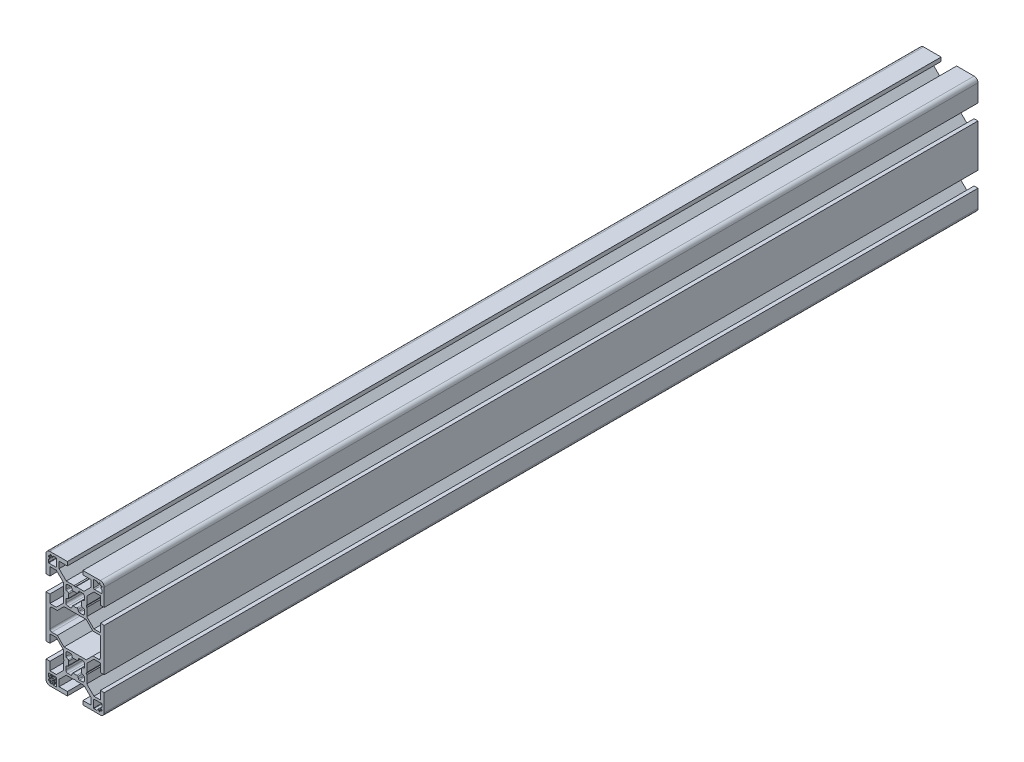
SolidWorks part; units mm, degrees
material "6063-T5"
ref_plane "Piano frontale" through (0, 0, 0) normal (0, 0, 1) x (1, 0, 0)
ref_plane "Piano superiore" through (0, 0, 0) normal (0, 1, 0) x (1, 0, 0)
ref_plane "Piano destro" through (0, 0, 0) normal (1, 0, 0) x (0, 0, -1)
ref_plane "Plane1" through (0, 0, -450) normal (0, 0, -1) x (-1, 0, 0)
sketch "Sketch1" plane through (0, 0, -450) normal (0, 0, -1) x (-1, 0, 0)
  line L0 (12.9, 28.5) -> (12.9, 28.2)
  line L1 (13.2, 27.9) -> (13.5, 27.9)
  line L2 (13.8, 27.6) -> (13.8, 27.4)
  line L3 (13.6, 27.2) -> (13.43, 27.2)
  line L4 (13.23, 27) -> (13.23, 26.6)
  line L5 (13.43, 26.4) -> (13.6, 26.4)
  line L6 (13.8, 26.2) -> (13.8, 24.7)
  line L7 (13.6, 24.5) -> (10, 24.5)
  line L8 (9.5, 25) -> (9.5, 28.6)
  line L9 (9.7, 28.8) -> (11.2, 28.8)
  line L10 (11.4, 28.6) -> (11.4, 28.43)
  line L11 (11.6, 28.23) -> (12, 28.23)
  line L12 (12.2, 28.43) -> (12.2, 28.6)
  line L13 (12.4, 28.8) -> (12.6, 28.8)
  line L14 (9.5, -28.6) -> (9.5, -25)
  line L15 (10, -24.5) -> (13.6, -24.5)
  line L16 (13.8, -24.7) -> (13.8, -26.2)
  line L17 (13.6, -26.4) -> (13.43, -26.4)
  line L18 (13.23, -26.6) -> (13.23, -27)
  line L19 (13.43, -27.2) -> (13.6, -27.2)
  line L20 (13.8, -27.4) -> (13.8, -27.6)
  line L21 (13.5, -27.9) -> (13.2, -27.9)
  line L22 (12.9, -28.2) -> (12.9, -28.5)
  line L23 (12.6, -28.8) -> (12.4, -28.8)
  line L24 (12.2, -28.6) -> (12.2, -28.43)
  line L25 (12, -28.23) -> (11.6, -28.23)
  line L26 (11.4, -28.43) -> (11.4, -28.6)
  line L27 (11.2, -28.8) -> (9.7, -28.8)
  line L28 (-5.7172, 9) -> (5.7172, 9)
  line L29 (9.1672, 5.55) -> (12, 5.55)
  line L30 (13, 4.55) -> (13, -4.55)
  line L31 (12, -5.55) -> (9.1672, -5.55)
  line L32 (5.7172, -9) -> (-5.7172, -9)
  line L33 (-9.1672, -5.55) -> (-12, -5.55)
  line L34 (-13, -4.55) -> (-13, 5.55)
  line L35 (-13, 5.55) -> (-9.1672, 5.55)
  line L36 (-11.2, 28.8) -> (-9.7, 28.8)
  line L37 (-9.5, 28.6) -> (-9.5, 25)
  line L38 (-10, 24.5) -> (-13.6, 24.5)
  line L39 (-13.8, 24.7) -> (-13.8, 26.2)
  line L40 (-13.6, 26.4) -> (-13.43, 26.4)
  line L41 (-13.23, 26.6) -> (-13.23, 27)
  line L42 (-13.43, 27.2) -> (-13.6, 27.2)
  line L43 (-13.8, 27.4) -> (-13.8, 27.6)
  line L44 (-13.5, 27.9) -> (-13.2, 27.9)
  line L45 (-12.9, 28.2) -> (-12.9, 28.5)
  line L46 (-12.6, 28.8) -> (-12.4, 28.8)
  line L47 (-12.2, 28.6) -> (-12.2, 28.43)
  line L48 (-12, 28.23) -> (-11.6, 28.23)
  line L49 (-11.4, 28.43) -> (-11.4, 28.6)
  line L50 (-13.8, -26.2) -> (-13.8, -24.7)
  line L51 (-13.6, -24.5) -> (-10, -24.5)
  line L52 (-9.5, -25) -> (-9.5, -28.6)
  line L53 (-9.7, -28.8) -> (-11.2, -28.8)
  line L54 (-11.4, -28.6) -> (-11.4, -28.43)
  line L55 (-11.6, -28.23) -> (-12, -28.23)
  line L56 (-12.2, -28.43) -> (-12.2, -28.6)
  line L57 (-12.4, -28.8) -> (-12.6, -28.8)
  line L58 (-12.9, -28.5) -> (-12.9, -28.2)
  line L59 (-13.2, -27.9) -> (-13.5, -27.9)
  line L60 (-13.8, -27.6) -> (-13.8, -27.4)
  line L61 (-13.6, -27.2) -> (-13.43, -27.2)
  line L62 (-13.23, -27) -> (-13.23, -26.6)
  line L63 (-13.43, -26.4) -> (-13.6, -26.4)
  line L64 (4.8, 18.8) -> (4.8, 17.2312)
  line L65 (4.4833, 16.766) -> (3.5987, 16.4176)
  line L66 (3.5987, 13.5824) -> (4.4833, 13.234)
  line L67 (4.8, 12.7688) -> (4.8, 11.2)
  line L68 (3.8, 10.2) -> (2.2312, 10.2)
  line L69 (1.766, 10.5167) -> (1.4176, 11.4013)
  line L70 (-1.4176, 11.4013) -> (-1.766, 10.5167)
  line L71 (-2.2312, 10.2) -> (-3.8, 10.2)
  line L72 (-4.8, 11.2) -> (-4.8, 12.7688)
  line L73 (-4.4833, 13.234) -> (-3.5987, 13.5824)
  line L74 (-3.5987, 16.4176) -> (-4.4833, 16.766)
  line L75 (-4.8, 17.2312) -> (-4.8, 18.8)
  line L76 (-3.8, 19.8) -> (-2.2312, 19.8)
  line L77 (1.4176, 18.5987) -> (1.766, 19.4833)
  line L78 (2.2312, 19.8) -> (3.8, 19.8)
  line L79 (4.8, -17.2312) -> (4.8, -18.8)
  line L80 (3.8, -19.8) -> (2.2312, -19.8)
  line L81 (-1.4176, -18.5987) -> (-1.766, -19.4833)
  line L82 (-2.2312, -19.8) -> (-3.8, -19.8)
  line L83 (-4.8, -18.8) -> (-4.8, -17.2312)
  line L84 (-4.4833, -16.766) -> (-3.5987, -16.4176)
  line L85 (-3.5987, -13.5824) -> (-4.4833, -13.234)
  line L86 (-4.8, -12.7688) -> (-4.8, -11.2)
  line L87 (-3.8, -10.2) -> (-2.2312, -10.2)
  line L88 (-1.766, -10.5167) -> (-1.4176, -11.4013)
  line L89 (1.4176, -11.4013) -> (1.766, -10.5167)
  line L90 (2.2312, -10.2) -> (3.8, -10.2)
  line L91 (4.8, -11.2) -> (4.8, -12.7688)
  line L92 (4.4833, -13.234) -> (3.5987, -13.5824)
  line L93 (3.5987, -16.4176) -> (4.4833, -16.766)
  line L94 (9.6642, -6.75) -> (13, -6.75)
  line L95 (13, -6.75) -> (13, -11)
  line L96 (13, -11) -> (15, -11)
  line L97 (15, -11) -> (15, 11)
  line L98 (15, 11) -> (13, 11)
  line L99 (13, 11) -> (13, 6.75)
  line L100 (13, 6.75) -> (9.6642, 6.75)
  line L101 (6, 10.4142) -> (6, 14.4804)
  line L102 (6, 14.4804) -> (5.7, 15)
  line L103 (5.7, 15) -> (6, 15.5196)
  line L104 (6, 15.5196) -> (6, 19.5858)
  line L105 (9.6642, 23.25) -> (13, 23.25)
  line L106 (13, 23.25) -> (13, 19)
  line L107 (13, 19) -> (15, 19)
  line L108 (15, 19) -> (15, 28)
  line L109 (13, 30) -> (4, 30)
  line L110 (4, 30) -> (4, 28)
  line L111 (4, 28) -> (8.25, 28)
  line L112 (8.25, 28) -> (8.25, 24.6642)
  line L113 (4.5858, 21) -> (0.5196, 21)
  line L114 (0.5196, 21) -> (0, 20.7)
  line L115 (0, 20.7) -> (-0.5196, 21)
  line L116 (-0.5196, 21) -> (-4.5858, 21)
  line L117 (-8.25, 24.6642) -> (-8.25, 28)
  line L118 (-8.25, 28) -> (-4, 28)
  line L119 (-4, 28) -> (-4, 30)
  line L120 (-4, 30) -> (-13, 30)
  line L121 (-15, 28) -> (-15, 19)
  line L122 (-15, 19) -> (-13, 19)
  line L123 (-13, 19) -> (-13, 23.25)
  line L124 (-13, 23.25) -> (-9.6642, 23.25)
  line L125 (-6, 19.5858) -> (-6, 15.5196)
  line L126 (-6, 15.5196) -> (-5.7, 15)
  line L127 (-5.7, 15) -> (-6, 14.4804)
  line L128 (-6, 14.4804) -> (-6, 10.4142)
  line L129 (-9.6642, 6.75) -> (-13, 6.75)
  line L130 (-13, 6.75) -> (-13, 11)
  line L131 (-13, 11) -> (-15, 11)
  line L132 (-15, 11) -> (-15, -11)
  line L133 (-15, -11) -> (-13, -11)
  line L134 (-13, -11) -> (-13, -6.75)
  line L135 (-13, -6.75) -> (-9.6642, -6.75)
  line L136 (-6, -10.4142) -> (-6, -14.4804)
  line L137 (-6, -14.4804) -> (-5.7, -15)
  line L138 (-5.7, -15) -> (-6, -15.5196)
  line L139 (-6, -15.5196) -> (-6, -19.5858)
  line L140 (-9.6642, -23.25) -> (-13, -23.25)
  line L141 (-13, -23.25) -> (-13, -19)
  line L142 (-13, -19) -> (-15, -19)
  line L143 (-15, -19) -> (-15, -28)
  line L144 (-13, -30) -> (-4, -30)
  line L145 (-4, -30) -> (-4, -28)
  line L146 (-4, -28) -> (-8.25, -28)
  line L147 (-8.25, -28) -> (-8.25, -24.6642)
  line L148 (-4.5858, -21) -> (-0.5196, -21)
  line L149 (-0.5196, -21) -> (0, -20.7)
  line L150 (0, -20.7) -> (0.5196, -21)
  line L151 (0.5196, -21) -> (4.5858, -21)
  line L152 (8.25, -24.6642) -> (8.25, -28)
  line L153 (8.25, -28) -> (4, -28)
  line L154 (4, -28) -> (4, -30)
  line L155 (4, -30) -> (13, -30)
  line L156 (15, -28) -> (15, -19)
  line L157 (15, -19) -> (13, -19)
  line L158 (13, -19) -> (13, -23.25)
  line L159 (13, -23.25) -> (9.6642, -23.25)
  line L160 (6, -19.5858) -> (6, -15.5196)
  line L161 (6, -15.5196) -> (5.7, -15)
  line L162 (5.7, -15) -> (6, -14.4804)
  line L163 (6, -14.4804) -> (6, -10.4142)
  arc A0 (12.9, 28.2) -> (13.2, 27.9) centre (13.2, 28.2) ccw
  arc A1 (13.5, 27.9) -> (13.8, 27.6) centre (13.5, 27.6) cw
  arc A2 (13.8, 27.4) -> (13.6, 27.2) centre (13.6, 27.4) cw
  arc A3 (13.43, 27.2) -> (13.23, 27) centre (13.43, 27) ccw
  arc A4 (13.23, 26.6) -> (13.43, 26.4) centre (13.43, 26.6) ccw
  arc A5 (13.6, 26.4) -> (13.8, 26.2) centre (13.6, 26.2) cw
  arc A6 (13.8, 24.7) -> (13.6, 24.5) centre (13.6, 24.7) cw
  arc A7 (10, 24.5) -> (9.5, 25) centre (10, 25) cw
  arc A8 (9.5, 28.6) -> (9.7, 28.8) centre (9.7, 28.6) cw
  arc A9 (11.2, 28.8) -> (11.4, 28.6) centre (11.2, 28.6) cw
  arc A10 (11.4, 28.43) -> (11.6, 28.23) centre (11.6, 28.43) ccw
  arc A11 (12, 28.23) -> (12.2, 28.43) centre (12, 28.43) ccw
  arc A12 (12.2, 28.6) -> (12.4, 28.8) centre (12.4, 28.6) cw
  arc A13 (12.6, 28.8) -> (12.9, 28.5) centre (12.6, 28.5) cw
  arc A14 (9.5, -25) -> (10, -24.5) centre (10, -25) cw
  arc A15 (13.6, -24.5) -> (13.8, -24.7) centre (13.6, -24.7) cw
  arc A16 (13.8, -26.2) -> (13.6, -26.4) centre (13.6, -26.2) cw
  arc A17 (13.43, -26.4) -> (13.23, -26.6) centre (13.43, -26.6) ccw
  arc A18 (13.23, -27) -> (13.43, -27.2) centre (13.43, -27) ccw
  arc A19 (13.6, -27.2) -> (13.8, -27.4) centre (13.6, -27.4) cw
  arc A20 (13.8, -27.6) -> (13.5, -27.9) centre (13.5, -27.6) cw
  arc A21 (13.2, -27.9) -> (12.9, -28.2) centre (13.2, -28.2) ccw
  arc A22 (12.9, -28.5) -> (12.6, -28.8) centre (12.6, -28.5) cw
  arc A23 (12.4, -28.8) -> (12.2, -28.6) centre (12.4, -28.6) cw
  arc A24 (12.2, -28.43) -> (12, -28.23) centre (12, -28.43) ccw
  arc A25 (11.6, -28.23) -> (11.4, -28.43) centre (11.6, -28.43) ccw
  arc A26 (11.4, -28.6) -> (11.2, -28.8) centre (11.2, -28.6) cw
  arc A27 (9.7, -28.8) -> (9.5, -28.6) centre (9.7, -28.6) cw
  arc A28 (12, 5.55) -> (13, 4.55) centre (12, 4.55) cw
  arc A29 (13, -4.55) -> (12, -5.55) centre (12, -4.55) cw
  arc A30 (-12, -5.55) -> (-13, -4.55) centre (-12, -4.55) cw
  arc A31 (-11.4, 28.6) -> (-11.2, 28.8) centre (-11.2, 28.6) cw
  arc A32 (-9.7, 28.8) -> (-9.5, 28.6) centre (-9.7, 28.6) cw
  arc A33 (-9.5, 25) -> (-10, 24.5) centre (-10, 25) cw
  arc A34 (-13.6, 24.5) -> (-13.8, 24.7) centre (-13.6, 24.7) cw
  arc A35 (-13.8, 26.2) -> (-13.6, 26.4) centre (-13.6, 26.2) cw
  arc A36 (-13.43, 26.4) -> (-13.23, 26.6) centre (-13.43, 26.6) ccw
  arc A37 (-13.23, 27) -> (-13.43, 27.2) centre (-13.43, 27) ccw
  arc A38 (-13.6, 27.2) -> (-13.8, 27.4) centre (-13.6, 27.4) cw
  arc A39 (-13.8, 27.6) -> (-13.5, 27.9) centre (-13.5, 27.6) cw
  arc A40 (-13.2, 27.9) -> (-12.9, 28.2) centre (-13.2, 28.2) ccw
  arc A41 (-12.9, 28.5) -> (-12.6, 28.8) centre (-12.6, 28.5) cw
  arc A42 (-12.4, 28.8) -> (-12.2, 28.6) centre (-12.4, 28.6) cw
  arc A43 (-12.2, 28.43) -> (-12, 28.23) centre (-12, 28.43) ccw
  arc A44 (-11.6, 28.23) -> (-11.4, 28.43) centre (-11.6, 28.43) ccw
  arc A45 (-13.8, -24.7) -> (-13.6, -24.5) centre (-13.6, -24.7) cw
  arc A46 (-10, -24.5) -> (-9.5, -25) centre (-10, -25) cw
  arc A47 (-9.5, -28.6) -> (-9.7, -28.8) centre (-9.7, -28.6) cw
  arc A48 (-11.2, -28.8) -> (-11.4, -28.6) centre (-11.2, -28.6) cw
  arc A49 (-11.4, -28.43) -> (-11.6, -28.23) centre (-11.6, -28.43) ccw
  arc A50 (-12, -28.23) -> (-12.2, -28.43) centre (-12, -28.43) ccw
  arc A51 (-12.2, -28.6) -> (-12.4, -28.8) centre (-12.4, -28.6) cw
  arc A52 (-12.6, -28.8) -> (-12.9, -28.5) centre (-12.6, -28.5) cw
  arc A53 (-12.9, -28.2) -> (-13.2, -27.9) centre (-13.2, -28.2) ccw
  arc A54 (-13.5, -27.9) -> (-13.8, -27.6) centre (-13.5, -27.6) cw
  arc A55 (-13.8, -27.4) -> (-13.6, -27.2) centre (-13.6, -27.4) cw
  arc A56 (-13.43, -27.2) -> (-13.23, -27) centre (-13.43, -27) ccw
  arc A57 (-13.23, -26.6) -> (-13.43, -26.4) centre (-13.43, -26.6) ccw
  arc A58 (-13.6, -26.4) -> (-13.8, -26.2) centre (-13.6, -26.2) cw
  arc A59 (4.8, 17.2312) -> (4.4833, 16.766) centre (4.3, 17.2312) cw
  arc A60 (3.5987, 16.4176) -> (3.2971, 15.8303) centre (3.7819, 15.9524) ccw
  arc A61 (3.2971, 15.8303) -> (3.2971, 14.1697) centre (0, 15) cw
  arc A62 (3.2971, 14.1697) -> (3.5987, 13.5824) centre (3.7819, 14.0476) ccw
  arc A63 (4.4833, 13.234) -> (4.8, 12.7688) centre (4.3, 12.7688) cw
  arc A64 (4.8, 11.2) -> (3.8, 10.2) centre (3.8, 11.2) cw
  arc A65 (2.2312, 10.2) -> (1.766, 10.5167) centre (2.2312, 10.7) cw
  arc A66 (1.4176, 11.4013) -> (0.8303, 11.7029) centre (0.9524, 11.2181) ccw
  arc A67 (0.8303, 11.7029) -> (-0.8303, 11.7029) centre (0, 15) cw
  arc A68 (-0.8303, 11.7029) -> (-1.4176, 11.4013) centre (-0.9524, 11.2181) ccw
  arc A69 (-1.766, 10.5167) -> (-2.2312, 10.2) centre (-2.2312, 10.7) cw
  arc A70 (-3.8, 10.2) -> (-4.8, 11.2) centre (-3.8, 11.2) cw
  arc A71 (-4.8, 12.7688) -> (-4.4833, 13.234) centre (-4.3, 12.7688) cw
  arc A72 (-3.5987, 13.5824) -> (-3.2971, 14.1697) centre (-3.7819, 14.0476) ccw
  arc A73 (-3.2971, 14.1697) -> (-3.2971, 15.8303) centre (0, 15) cw
  arc A74 (-3.2971, 15.8303) -> (-3.5987, 16.4176) centre (-3.7819, 15.9524) ccw
  arc A75 (-4.4833, 16.766) -> (-4.8, 17.2312) centre (-4.3, 17.2312) cw
  arc A76 (-4.8, 18.8) -> (-3.8, 19.8) centre (-3.8, 18.8) cw
  arc A77 (-2.2312, 19.8) -> (-1.766, 19.4833) centre (-2.2312, 19.3) cw
  arc A78 (-1.4176, 18.5987) -> (-0.8303, 18.2971) centre (-0.9524, 18.7819) ccw
  arc A79 (-0.8303, 18.2971) -> (0.8303, 18.2971) centre (0, 15) cw
  arc A80 (0.8303, 18.2971) -> (1.4176, 18.5987) centre (0.9524, 18.7819) ccw
  arc A81 (1.766, 19.4833) -> (2.2312, 19.8) centre (2.2312, 19.3) cw
  arc A82 (3.8, 19.8) -> (4.8, 18.8) centre (3.8, 18.8) cw
  arc A83 (4.8, -18.8) -> (3.8, -19.8) centre (3.8, -18.8) cw
  arc A84 (2.2312, -19.8) -> (1.766, -19.4833) centre (2.2312, -19.3) cw
  arc A85 (1.4176, -18.5987) -> (0.8303, -18.2971) centre (0.9524, -18.7819) ccw
  arc A86 (0.8303, -18.2971) -> (-0.8303, -18.2971) centre (0, -15) cw
  arc A87 (-0.8303, -18.2971) -> (-1.4176, -18.5987) centre (-0.9524, -18.7819) ccw
  arc A88 (-1.766, -19.4833) -> (-2.2312, -19.8) centre (-2.2312, -19.3) cw
  arc A89 (-3.8, -19.8) -> (-4.8, -18.8) centre (-3.8, -18.8) cw
  arc A90 (-4.8, -17.2312) -> (-4.4833, -16.766) centre (-4.3, -17.2312) cw
  arc A91 (-3.5987, -16.4176) -> (-3.2971, -15.8303) centre (-3.7819, -15.9524) ccw
  arc A92 (-3.2971, -15.8303) -> (-3.2971, -14.1697) centre (0, -15) cw
  arc A93 (-3.2971, -14.1697) -> (-3.5987, -13.5824) centre (-3.7819, -14.0476) ccw
  arc A94 (-4.4833, -13.234) -> (-4.8, -12.7688) centre (-4.3, -12.7688) cw
  arc A95 (-4.8, -11.2) -> (-3.8, -10.2) centre (-3.8, -11.2) cw
  arc A96 (-2.2312, -10.2) -> (-1.766, -10.5167) centre (-2.2312, -10.7) cw
  arc A97 (-1.4176, -11.4013) -> (-0.8303, -11.7029) centre (-0.9524, -11.2181) ccw
  arc A98 (-0.8303, -11.7029) -> (0.8303, -11.7029) centre (0, -15) cw
  arc A99 (0.8303, -11.7029) -> (1.4176, -11.4013) centre (0.9524, -11.2181) ccw
  arc A100 (1.766, -10.5167) -> (2.2312, -10.2) centre (2.2312, -10.7) cw
  arc A101 (3.8, -10.2) -> (4.8, -11.2) centre (3.8, -11.2) cw
  arc A102 (4.8, -12.7688) -> (4.4833, -13.234) centre (4.3, -12.7688) cw
  arc A103 (3.5987, -13.5824) -> (3.2971, -14.1697) centre (3.7819, -14.0476) ccw
  arc A104 (3.2971, -14.1697) -> (3.2971, -15.8303) centre (0, -15) cw
  arc A105 (3.2971, -15.8303) -> (3.5987, -16.4176) centre (3.7819, -15.9524) ccw
  arc A106 (4.4833, -16.766) -> (4.8, -17.2312) centre (4.3, -17.2312) cw
  arc A107 (15, 28) -> (13, 30) centre (13, 28) ccw
  arc A108 (-13, 30) -> (-15, 28) centre (-13, 28) ccw
  arc A109 (-15, -28) -> (-13, -30) centre (-13, -28) ccw
  arc A110 (13, -30) -> (15, -28) centre (13, -28) ccw
  spline S0 degree 3 poles (5.7172, 9) (6.8672, 7.85) (8.0172, 6.7) (9.1672, 5.55) knots 0 0 0 0 1 1 1 1
  spline S1 degree 3 poles (9.1672, -5.55) (8.0172, -6.7) (6.8672, -7.85) (5.7172, -9) knots 0 0 0 0 1 1 1 1
  spline S2 degree 3 poles (-5.7172, -9) (-6.8672, -7.85) (-8.0172, -6.7) (-9.1672, -5.55) knots 0 0 0 0 1 1 1 1
  spline S3 degree 3 poles (-9.1672, 5.55) (-8.0172, 6.7) (-6.8672, 7.85) (-5.7172, 9) knots 0 0 0 0 1 1 1 1
  spline S4 degree 3 poles (-1.766, 19.4833) (-1.6499, 19.1884) (-1.5337, 18.8935) (-1.4176, 18.5987) knots 0 0 0 0 1 1 1 1
  spline S5 degree 3 poles (1.766, -19.4833) (1.6499, -19.1884) (1.5337, -18.8935) (1.4176, -18.5987) knots 0 0 0 0 1 1 1 1
  spline S6 degree 3 poles (6, -10.4142) (7.2214, -9.1928) (8.4428, -7.9714) (9.6642, -6.75) knots 0 0 0 0 1 1 1 1
  spline S7 degree 3 poles (9.6642, 6.75) (8.4428, 7.9714) (7.2214, 9.1928) (6, 10.4142) knots 0 0 0 0 1 1 1 1
  spline S8 degree 3 poles (6, 19.5858) (7.2214, 20.8072) (8.4428, 22.0286) (9.6642, 23.25) knots 0 0 0 0 1 1 1 1
  spline S9 degree 3 poles (8.25, 24.6642) (7.0286, 23.4428) (5.8072, 22.2214) (4.5858, 21) knots 0 0 0 0 1 1 1 1
  spline S10 degree 3 poles (-4.5858, 21) (-5.8072, 22.2214) (-7.0286, 23.4428) (-8.25, 24.6642) knots 0 0 0 0 1 1 1 1
  spline S11 degree 3 poles (-9.6642, 23.25) (-8.4428, 22.0286) (-7.2214, 20.8072) (-6, 19.5858) knots 0 0 0 0 1 1 1 1
  spline S12 degree 3 poles (-6, 10.4142) (-7.2214, 9.1928) (-8.4428, 7.9714) (-9.6642, 6.75) knots 0 0 0 0 1 1 1 1
  spline S13 degree 3 poles (-9.6642, -6.75) (-8.4428, -7.9714) (-7.2214, -9.1928) (-6, -10.4142) knots 0 0 0 0 1 1 1 1
  spline S14 degree 3 poles (-6, -19.5858) (-7.2214, -20.8072) (-8.4428, -22.0286) (-9.6642, -23.25) knots 0 0 0 0 1 1 1 1
  spline S15 degree 3 poles (-8.25, -24.6642) (-7.0286, -23.4428) (-5.8072, -22.2214) (-4.5858, -21) knots 0 0 0 0 1 1 1 1
  spline S16 degree 3 poles (4.5858, -21) (5.8072, -22.2214) (7.0286, -23.4428) (8.25, -24.6642) knots 0 0 0 0 1 1 1 1
  spline S17 degree 3 poles (9.6642, -23.25) (8.4428, -22.0286) (7.2214, -20.8072) (6, -19.5858) knots 0 0 0 0 1 1 1 1
extrude "Extrude1" add sketch "Sketch1" against normal blind 450
